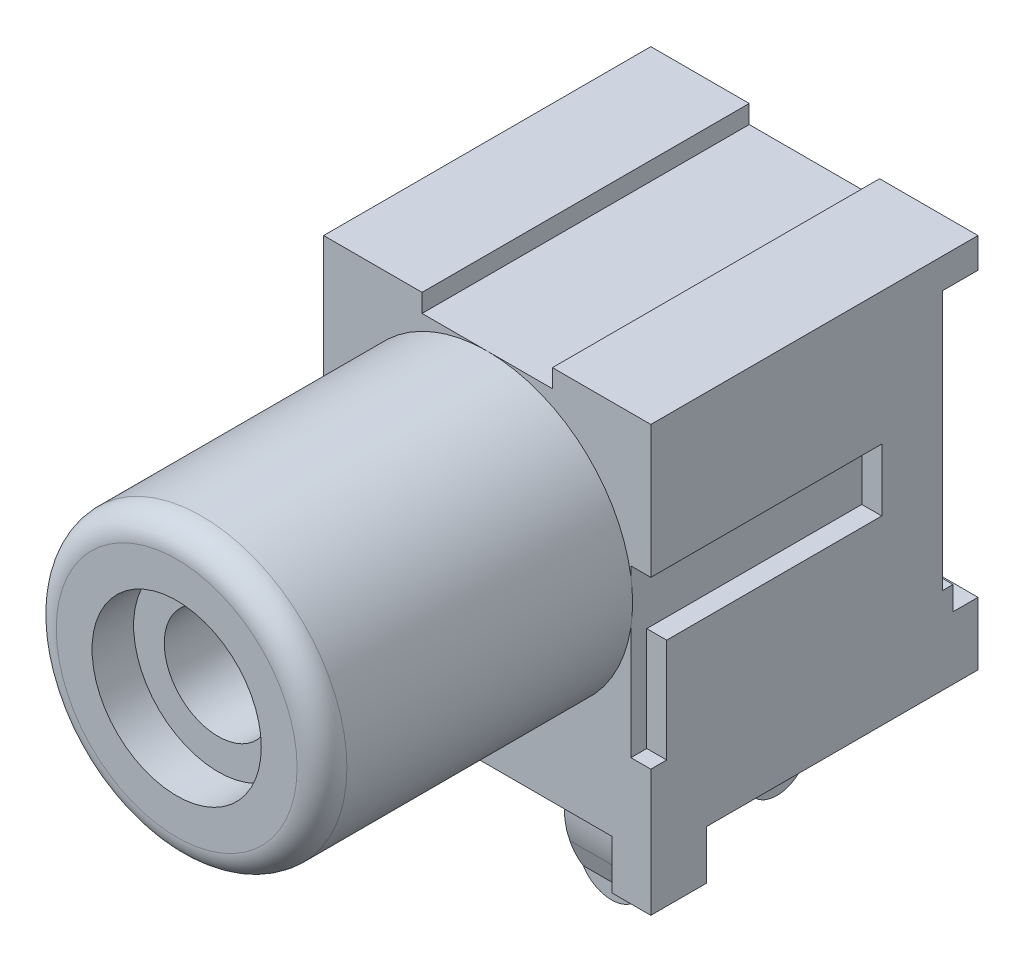
SolidWorks part; units mm, degrees
ref_plane "Front Plane" through (0, 0, 0) normal (0, 0, 1) x (1, 0, 0)
ref_plane "Top Plane" through (0, 0, 0) normal (0, 1, 0) x (1, 0, 0)
ref_plane "Right Plane" through (0, 0, 0) normal (1, 0, 0) x (0, 0, -1)
sketch "Sketch1" plane through (0, 0, 0) normal (0, 0, 1) x (1, 0, 0)
  line L1 (-5.0038, 0) -> (5.0038, 0)
  line L2 (-5.0038, 0) -> (-5.0038, 13.0048)
  line L3 (-5.0038, 13.0048) -> (5.0038, 13.0048)
  line L4 (5.0038, 0) -> (5.0038, 13.0048)
  dimension "D1" = 10.0076
  dimension "D2" = 13.0048
extrude "Extrude1" add sketch "Sketch1" against normal blind 10.0076
ref_plane "Plane1" through (0, 8.001, 0) normal (0, 1, 0) x (-1, 0, 0)
sketch "Sketch2" plane through (0, 0, 0) normal (0, 0, 1) x (1, 0, 0)
  line L2 (0, -9.3459) -> (0, 9.3459) construction
  line L3 (-5.0038, 0) -> (5.0038, 0) construction
  circle A0 centre (0, 8.001) radius 4.445
  dimension "D2" = 8.89
  dimension "D1" = 8.001
extrude "Extrude2" add sketch "Sketch2" along normal blind 9.4996
fillet "Fillet1" radius 0.762 1 edges at (4.445, 8.001, 9.4996)
sketch "Sketch3" plane through (0, 0, 9.4996) normal (0, 0, 1) x (1, 0, 0)
  line L0 (5.5042, 8.001) -> (-5.5042, 8.001) construction
  line L1 (-5.0038, 13.0048) -> (-5.0038, 0) construction
  circle A0 centre (0, 8.001) radius 1.6497
  dimension "D1" = 3.2995
  dimension "D2" = 5.0038
extrude "Cut-Extrude1" cut sketch "Sketch3" against normal up to surface (9.4996 mm away) up to face at (0, 6.5024, 0)
sketch "Sketch4" plane through (5.0038, 0, 0) normal (1, 0, 0) x (0, 0, -1)
  line L0 (5.5042, 8.001) -> (-5.5042, 8.001) construction
  line L1 (0, 8.9535) -> (7.064, 8.9535)
  line L2 (0, 8.9535) -> (0, 3.8728)
  line L3 (0.4849, 7.0485) -> (7.064, 7.0485)
  line L4 (7.064, 8.9535) -> (7.064, 7.0485)
  line L8 (0, 3.8728) -> (0.4849, 3.8728)
  line L9 (0.4849, 7.0485) -> (0.4849, 3.8728)
  dimension "D1" = 1.905
  dimension "D2" = 0.9525
extrude "Cut-Extrude2" cut sketch "Sketch4" against normal blind 0.6096
sketch "Sketch5" plane through (5.0038, 0, 0) normal (1, 0, 0) x (0, 0, -1)
  line L0 (10.0076, 0) -> (10.0076, 13.0048) construction
  line L1 (10.0076, 12.0849) -> (8.9254, 12.0849)
  line L2 (10.0076, 12.0849) -> (10.0076, 4.143)
  line L3 (10.0076, 4.143) -> (8.9254, 4.143)
  line L4 (8.9254, 12.0849) -> (8.9254, 4.143)
extrude "Cut-Extrude3" cut sketch "Sketch5" against normal through all
sketch "Sketch6" plane through (0, 0, 0) normal (0, 0, 1) x (1, 0, 0)
  line L0 (-5.0038, 0) -> (5.0038, 0) construction
  line L1 (-3.81, 0) -> (3.81, 0)
  line L2 (-3.81, 0) -> (-3.81, 1.4986)
  line L3 (-3.81, 1.4986) -> (3.81, 1.4986)
  line L4 (3.81, 0) -> (3.81, 1.4986)
  line L5 (5.5042, 8.001) -> (-5.5042, 8.001) construction
  dimension "D1" = 7.62
  dimension "D2" = 3.81
  dimension "D3" = 6.5024
extrude "Cut-Extrude4" cut sketch "Sketch6" against normal through all
sketch "Sketch7" plane through (0, 0, 9.4996) normal (0, 0, 1) x (1, 0, 0)
  line L0 (5.5042, 8.001) -> (-5.5042, 8.001) construction
  line L1 (-5.0038, 13.0048) -> (-5.0038, 0) construction
  circle A0 centre (0, 8.001) radius 2.588
  dimension "D1" = 5.0038
extrude "Cut-Extrude5" cut sketch "Sketch7" against normal blind 1.27
sketch "Sketch8" plane through (0, 0, 0) normal (0, 0, 1) x (1, 0, 0)
  line L0 (5.0038, 13.0048) -> (-5.0038, 13.0048) construction
  line L1 (-1.9939, 13.0048) -> (1.9939, 13.0048)
  line L2 (-1.9939, 13.0048) -> (-1.9939, 12.446)
  line L3 (-1.9939, 12.446) -> (1.9939, 12.446)
  line L4 (1.9939, 13.0048) -> (1.9939, 12.446)
  line L5 (0, -9.3459) -> (0, 9.3459) construction
  arc A0 (4.3942, 8.6711) -> (4.3942, 7.3309) centre (0, 8.001) ccw construction
  dimension "D1" = 3.9878
  dimension "D2" = 1.9939
extrude "Cut-Extrude6" cut sketch "Sketch8" against normal through all
mirror "Mirror1" about plane through (0, 0, 0) normal (1, 0, 0) of "Cut-Extrude2"
sketch "Sketch10" plane through (5.0038, 0, 0) normal (1, 0, 0) x (0, 0, -1)
  line L0 (5.5042, 8.001) -> (-5.5042, 8.001) construction
  line L1 (10.0076, 0) -> (1.7049, 0)
  line L2 (10.0076, 0) -> (10.0076, 1.4986)
  line L3 (10.0076, 1.4986) -> (1.7049, 1.4986)
  line L4 (1.7049, 0) -> (1.7049, 1.4986)
  dimension "D1" = 6.5024
extrude "Cut-Extrude8" cut sketch "Sketch10" against normal through all
sketch "Sketch11" plane through (5.0038, 0, 0) normal (1, 0, 0) x (0, 0, -1)
  line L1 (10.0076, 4.143) -> (9.2437, 4.143)
  line L2 (10.0076, 4.143) -> (10.0076, 3.4214)
  line L3 (10.0076, 3.4214) -> (9.2437, 3.4214)
  line L4 (9.2437, 4.143) -> (9.2437, 3.4214)
extrude "Cut-Extrude9" cut sketch "Sketch11" against normal through all
ref_plane "Plane2" through (0, 0, -3.9878) normal (0, 0, 1) x (1, 0, 0)
sketch "Sketch12" plane through (0, 1.4986, 0) normal (0, -1, 0) x (1, 0, 0)
  line L0 (0, -9.3459) -> (0, 9.3459) construction
  line L1 (-1.0033, -3.7973) -> (1.0033, -3.7973)
  line L2 (-1.0033, -3.7973) -> (-1.0033, -4.1783)
  line L3 (-1.0033, -4.1783) -> (1.0033, -4.1783)
  line L4 (1.0033, -3.7973) -> (1.0033, -4.1783)
  line L5 (4.032, -3.9878) -> (-4.032, -3.9878) construction
  dimension "D1" = 2.0066
  dimension "D2" = 1.0033
  dimension "D3" = 0.381
  dimension "D4" = 0.1905
sketch "Sketch13" plane through (0, 0, 0) normal (1, 0, 0) x (0, 0, -1)
  line L0 (3.9878, 1.4986) -> (3.9878, 0.1182)
  line L1 (3.7973, 1.4986) -> (4.1783, 1.4986) construction
  line L2 (3.9878, 4.032) -> (3.9878, -4.032) construction
  line L4 (3.7089, -2.7232) -> (3.9878, -3.4798)
  line L6 (3.9878, -3.4798) -> (3.9878, -3.9878)
  line L7 (1.7049, 0) -> (0, 0) construction
  arc A0 (3.7089, -2.7232) -> (3.8905, -0.578) centre (6.0921, -1.8447) cw
  arc A1 (3.9878, 0.1182) -> (3.8905, -0.578) centre (1.4478, 0.1182) cw
  point P12 (3.3528, -1.7571)
  point P15 (3.9878, -0.1149)
  dimension "D3" = 2.54
  dimension "D1" = 3.9878
  dimension "D2" = 0.635
  dimension "D4" = 0.508
sweep "Sweep1" add profiles "Sketch12" path "Sketch13"
fillet "Fillet2" radius 0.9906 2 edges at (1.0033, -3.9878, -3.9876) (-1.0033, -3.9878, -3.9876)
sketch "Sketch14" plane through (0, 0, 0) normal (1, 0, 0) x (0, 0, -1)
  line L0 (10.0076, 0) -> (9.0551, 0)
  line L1 (10.0076, 1.4986) -> (7.6289, 1.4986)
  line L2 (10.0076, 1.4986) -> (10.0076, 0)
  line L3 (10.0076, 1.4986) -> (10.0076, 3.4214) construction
  line L4 (7.6289, 1.4986) -> (7.6289, -2.525)
  line L5 (9.0551, 0) -> (9.0551, -1.4595)
  line L6 (9.0551, -1.4595) -> (10.0076, -1.9505)
  line L7 (10.0076, -1.9505) -> (9.4663, -3.0005)
  line L8 (10.0076, 1.4986) -> (1.7049, 1.4986) construction
  arc A0 (7.6289, -2.525) -> (9.4663, -3.0005) centre (8.6091, -2.525) ccw
  dimension "D1" = 2.3787
  dimension "D2" = 0.9525
extrude "Extrude3" add sketch "Sketch14" along normal mid plane 0.508
sketch "PCB-Hole Layout" plane through (0, 0, 0) normal (0, 1, 0) x (1, 0, 0)
  line L0 (-4.032, 3.9878) -> (4.032, 3.9878) construction
  line L1 (-1.1049, 4.5847) -> (1.1049, 4.5847)
  line L2 (-1.1049, 4.5847) -> (-1.1049, 3.3909)
  line L3 (-1.1049, 3.3909) -> (1.1049, 3.3909)
  line L4 (1.1049, 4.5847) -> (1.1049, 3.3909)
  line L5 (0, -9.3459) -> (0, 9.3459) construction
  line L7 (-0.5969, 9.5885) -> (0.5969, 9.5885)
  line L8 (-0.5969, 9.5885) -> (-0.5969, 7.3787)
  line L9 (-0.5969, 7.3787) -> (0.5969, 7.3787)
  line L10 (0.5969, 9.5885) -> (0.5969, 7.3787)
  dimension "D1" = 2.2098
  dimension "D2" = 1.1938
  dimension "D3" = 0.5969
  dimension "D4" = 1.1049
  dimension "D5" = 2.2098
  dimension "D6" = 1.1938
  dimension "D7" = 0.5969
  dimension "D8" = 2.794
